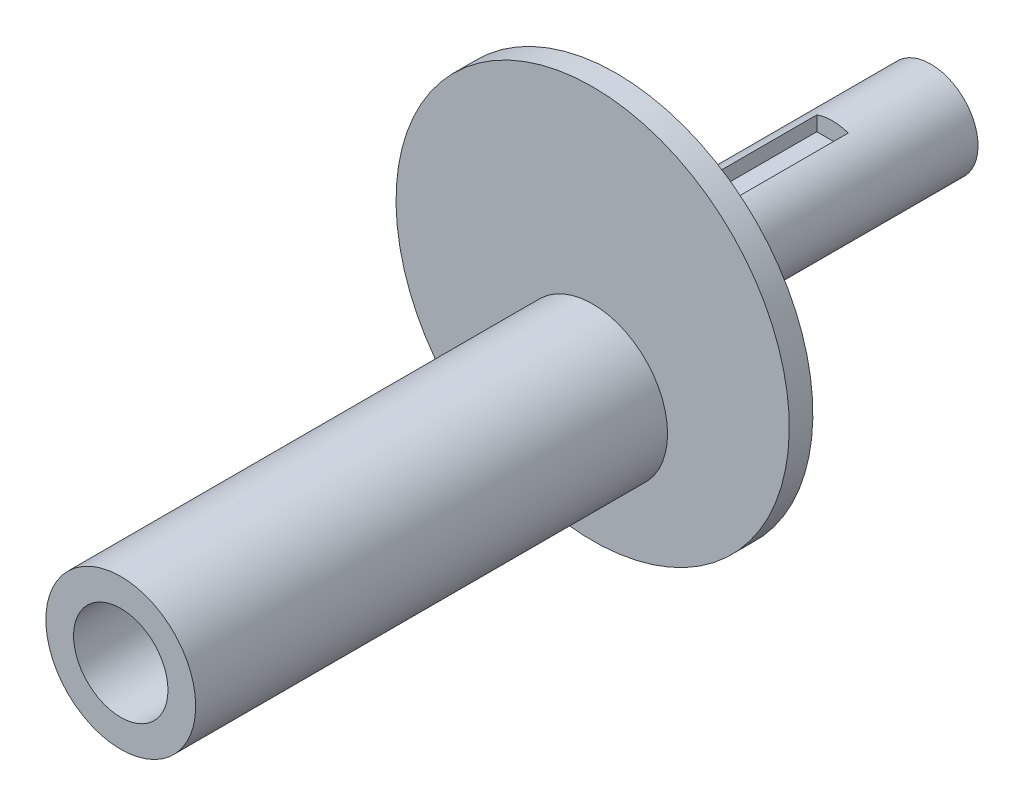
SolidWorks part; units mm, degrees
material "AISI 4340 Steel, normalized"
ref_plane "Front Plane" through (0, 0, 0) normal (0, 0, 1) x (1, 0, 0)
ref_plane "Top Plane" through (0, 0, 0) normal (0, 1, 0) x (1, 0, 0)
ref_plane "Right Plane" through (0, 0, 0) normal (1, 0, 0) x (0, 0, -1)
sketch "Sketch1" plane through (0, 0, 0) normal (1, 0, 0) x (0, 0, -1)
  line L0 (0, 0) -> (27.0901, 0) construction
  line L1 (0, 6) -> (0, 25)
  line L3 (-3, 25) -> (-3, 0)
  line L4 (27.0901, 0) -> (-3, 0)
  line L7 (0, 6) -> (40, 6)
  line L8 (40, 6) -> (40, 2.5)
  line L9 (0, 6) -> (0, -0.3127) construction
  line L10 (27.0901, 0) -> (28, 2.5)
  line L11 (28, 2.5) -> (40, 2.5)
  line L13 (0, 25) -> (-3, 25)
  dimension "D1" = 25
  dimension "D2" = 6
  dimension "D4" = 12
  dimension "30" = 40
  dimension "D6" = 2.5
  dimension "D7" = 110
  dimension "D8" = 3
revolve "Revolve1" add sketch "Sketch1" angle 360 about L4
sketch "Sketch2" plane through (0, 0, 3) normal (0, 0, 1) x (1, 0, 0)
  line L0 (0, 0) -> (0, -8.4375) construction
  circle A0 centre (0, -8.4375) radius 9.525
  circle A1 centre (0, -8.4375) radius 6
  dimension "D1" = 19.05
  dimension "D2" = 12
  dimension "D3" = 8.4375
extrude "Boss-Extrude1" add sketch "Sketch2" along normal blind 60
sketch "Sketch3" plane through (0, 0, 0) normal (0, 0, -1) x (-1, 0, 0)
  line L0 (0, 0) -> (0, 25.9724) construction
sketch "Sketch4" plane through (0, 0, 3) normal (0, 0, 1) x (1, 0, 0)
  line L0 (0, 0) -> (0, 11) construction
  line L1 (0, 0) -> (0, 117.8449) construction
sketch "Sketch5" plane through (0, 0, 0) normal (0, 0, -1) x (-1, 0, 0)
  line L0 (2, -7.8) -> (-2, -7.8)
  line L1 (-2, -7.8) -> (-2, -3.8)
  line L2 (-2, -3.8) -> (2, -3.8)
  line L3 (2, -3.8) -> (2, -7.8)
  dimension "D1" = 4
extrude "Cut-Extrude1" cut sketch "Sketch5" along normal blind 25 from offset 2.5
mirror "Mirror1" about plane through (0, 0, 0) normal (0, 1, 0) of "Cut-Extrude1"
